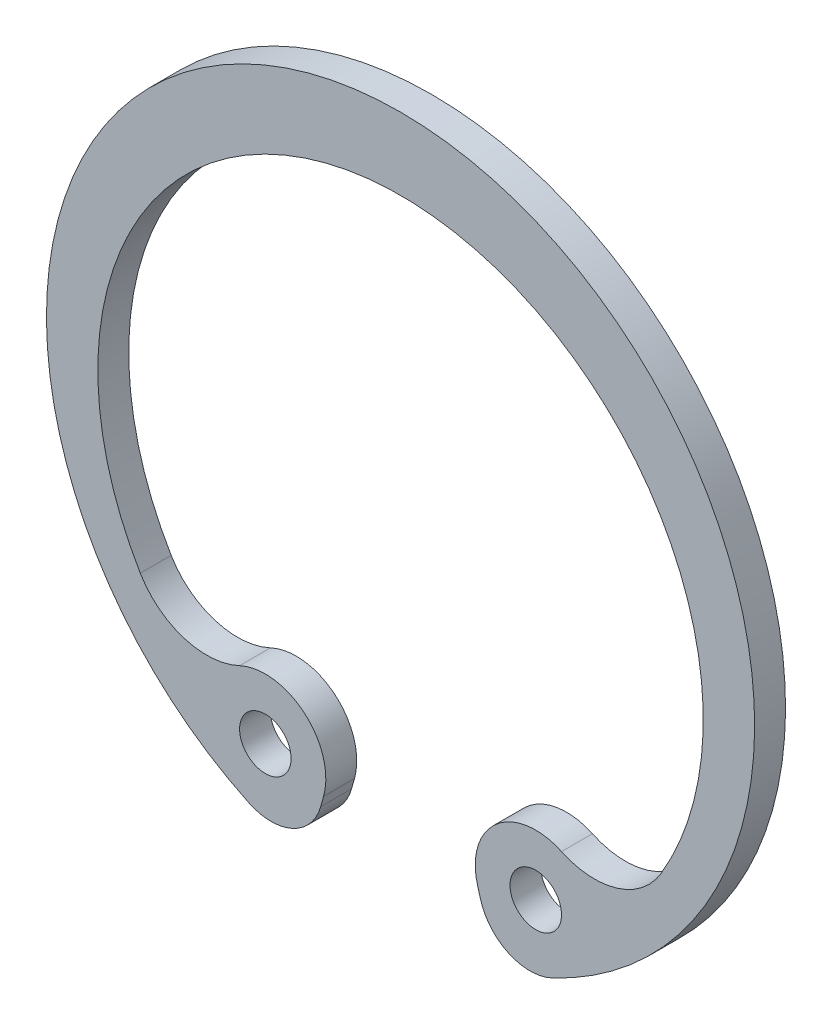
SolidWorks part; units mm, degrees
material "AISI 1020"
ref_plane "Спереди" through (0, 0, 0) normal (0, 0, 1) x (1, 0, 0)
ref_plane "Сверху" through (0, 0, 0) normal (0, 1, 0) x (1, 0, 0)
ref_plane "Справа" through (0, 0, 0) normal (1, 0, 0) x (0, 0, -1)
sketch "Эскиз1" plane through (0, 0, 0) normal (0, 0, 1) x (1, 0, 0)
  line L0 (0, -1000) -> (0, 49000) construction
  line L1 (0, 0) -> (5.85, -10.0747) construction
  line L2 (3.6215, -10.8206) -> (3.7553, -11.2204)
  line L3 (0, 11.2) -> (24, 11.2) construction
  arc A0 (6.5939, -12.3499) -> (0, 14) centre (0, 0) ccw
  circle A2 centre (5.85, -10.0747) radius 1
  arc A3 (6.7463, -7.9023) -> (3.6215, -10.8206) centre (5.85, -10.0747) ccw
  arc A4 (6.7463, -7.9023) -> (10.5206, -6.5721) centre (7.8904, -5.1291) ccw
  arc A5 (3.7553, -11.2204) -> (6.5939, -12.3499) centre (5.6519, -10.5856) ccw
  arc A6 (10.5206, -6.5721) -> (0, 11.2) centre (0, -0.8) ccw
  dimension "_d4" = 2
  dimension "_r1" = 3
  dimension "_r2" = 2
  dimension "_e" = 0.8
sketch "Эскиз2" plane through (0, 0, 0) normal (0, 0, 1) x (1, 0, 0)
  line L0 (0, -201000) -> (0, 249000) construction
  line L1 (-3.1033, -11.1624) -> (-2.9889, -10.7565)
  line L2 (3.6215, -10.8206) -> (3.7553, -11.2204) construction
  line L3 (0, 0) -> (6.5939, -12.3499) construction
  line L4 (0, 0) -> (-5.8842, -12.4273) construction
  line L5 (3.7553, -11.2204) -> (6.5939, -12.3499) construction
  line L6 (-5.8842, -12.4273) -> (-3.1033, -11.1624) construction
  line L7 (6.7463, -7.9023) -> (3.6215, -10.8206) construction
  line L8 (-6.2507, -7.9923) -> (-2.9889, -10.7565) construction
  line L9 (0, 13.75) -> (0, 14.95) construction
  circle A0 centre (0, 0) radius 13.75 construction
  circle A1 centre (0, 0) radius 13 construction
  circle A2 centre (0, 0) radius 7.8 construction
  arc A3 (0, 13.75) -> (-5.8842, -12.4273) centre (0, 0) ccw
  arc A4 (0, 10.95) -> (-10.1063, -6.8097) centre (0, -0.8054) ccw
  arc A5 (-5.8842, -12.4273) -> (-3.1033, -11.1624) centre (-5.0283, -10.6197) ccw
  arc A6 (-2.9889, -10.7565) -> (-6.2507, -7.9923) centre (-5.2508, -10.1189) ccw
  arc A7 (3.7553, -11.2204) -> (6.5939, -12.3499) centre (5.6519, -10.5856) ccw construction
  arc A8 (6.7463, -7.9023) -> (3.6215, -10.8206) centre (5.85, -10.0747) ccw construction
  arc A9 (-10.1063, -6.8097) -> (-6.2507, -7.9923) centre (-7.5271, -5.2774) ccw
  circle A10 centre (-5.2508, -10.1189) radius 1
  circle A11 centre (5.85, -10.0747) radius 1 construction
  arc A13 (6.7463, -7.9023) -> (10.5206, -6.5721) centre (7.8904, -5.1291) ccw construction
  dimension "D3" = 155.454
  dimension "_s" = 1.2
sketch "Эскиз3" plane through (0, 0, 0) normal (0, 0, 1) x (1, 0, 0)
  line L0 (-3.1033, -11.1624) -> (-2.9889, -10.7565) construction
  line L1 (-3.1033, -11.1624) -> (-2.9889, -10.7565)
  line L2 (0, -1000) -> (0, 49000) construction
  line L3 (0, -1000.0733) -> (0, 48999.9267) construction
  line L4 (3.1033, -11.1624) -> (2.9889, -10.7565)
  arc A0 (0, 10.95) -> (-10.1063, -6.8097) centre (0, -0.8054) ccw construction
  arc A1 (-10.1063, -6.8097) -> (-6.2507, -7.9923) centre (-7.5271, -5.2774) ccw construction
  arc A2 (-2.9889, -10.7565) -> (-6.2507, -7.9923) centre (-5.2508, -10.1189) ccw construction
  arc A3 (-5.8842, -12.4273) -> (-3.1033, -11.1624) centre (-5.0283, -10.6197) ccw construction
  arc A4 (0, 13.75) -> (-5.8842, -12.4273) centre (0, 0) ccw construction
  arc A5 (10.1063, -6.8097) -> (-10.1063, -6.8097) centre (0, -0.8054) ccw
  arc A6 (-10.1063, -6.8097) -> (-6.2507, -7.9923) centre (-7.5271, -5.2774) ccw
  arc A7 (-2.9889, -10.7565) -> (-6.2507, -7.9923) centre (-5.2508, -10.1189) ccw
  arc A8 (-5.8842, -12.4273) -> (-3.1033, -11.1624) centre (-5.0283, -10.6197) ccw
  arc A9 (5.8842, -12.4273) -> (-5.8842, -12.4273) centre (0, 0) ccw
  circle A10 centre (-5.2508, -10.1189) radius 1 construction
  circle A11 centre (-5.2508, -10.1189) radius 1
  circle A12 centre (5.2508, -10.1189) radius 1
  arc A13 (10.1063, -6.8097) -> (6.2507, -7.9923) centre (7.5271, -5.2774) cw
  arc A14 (2.9889, -10.7565) -> (6.2507, -7.9923) centre (5.2508, -10.1189) cw
  arc A15 (5.8842, -12.4273) -> (3.1033, -11.1624) centre (5.0283, -10.6197) cw
extrude "Бобышка-Вытянуть1" add sketch "Эскиз3" along normal blind 1.2
equation "\"D1@Эскиз1\"=\"_d3@Эскиз1\"/2"
equation "\"D3@Эскиз2\"=(\"D2@Эскиз2\"*2*\"D1@Эскиз2\"/360)/(\"_d1@Эскиз2\"/360)"
equation "\"D1@Бобышка-Вытянуть1\"= \"_s@Эскиз2\""
